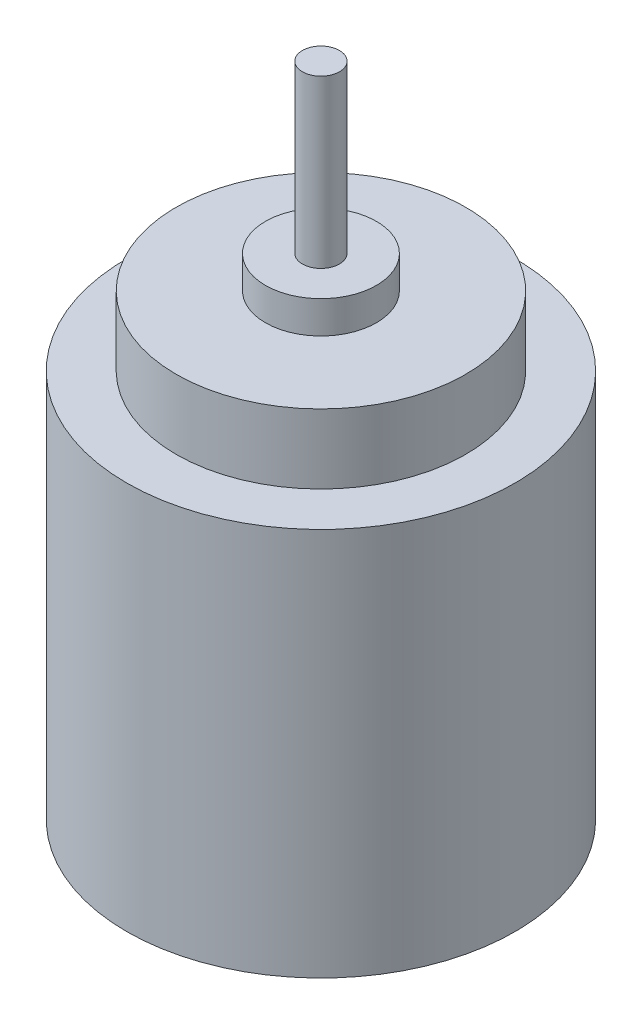
SolidWorks part; units mm, degrees
ref_plane "Front Plane" through (0, 0, 0) normal (0, 0, 1) x (1, 0, 0)
ref_plane "Top Plane" through (0, 0, 0) normal (0, 1, 0) x (1, 0, 0)
ref_plane "Right Plane" through (0, 0, 0) normal (1, 0, 0) x (0, 0, -1)
sketch "Sketch1" plane through (0, 0, 0) normal (0, 1, 0) x (1, 0, 0)
  circle A0 centre (0, 0) radius 10.5
  dimension "D1" = 21
extrude "Boss-Extrude1" add sketch "Sketch1" along normal blind 21
sketch "Sketch2" plane through (0, 21, 0) normal (0, 1, 0) x (1, 0, 0)
  circle A0 centre (0, 0) radius 7.825
  dimension "D1" = 15.65
extrude "Boss-Extrude2" add sketch "Sketch2" along normal blind 3.75
sketch "Sketch3" plane through (0, 24.75, 0) normal (0, 1, 0) x (1, 0, 0)
  circle A0 centre (0, 0) radius 3
  dimension "D1" = 6
extrude "Boss-Extrude3" add sketch "Sketch3" along normal blind 1.75
sketch "Sketch4" plane through (0, 26.5, 0) normal (0, 1, 0) x (1, 0, 0)
  circle A0 centre (0, 0) radius 1
  dimension "D1" = 2
extrude "Boss-Extrude4" add sketch "Sketch4" along normal blind 9
